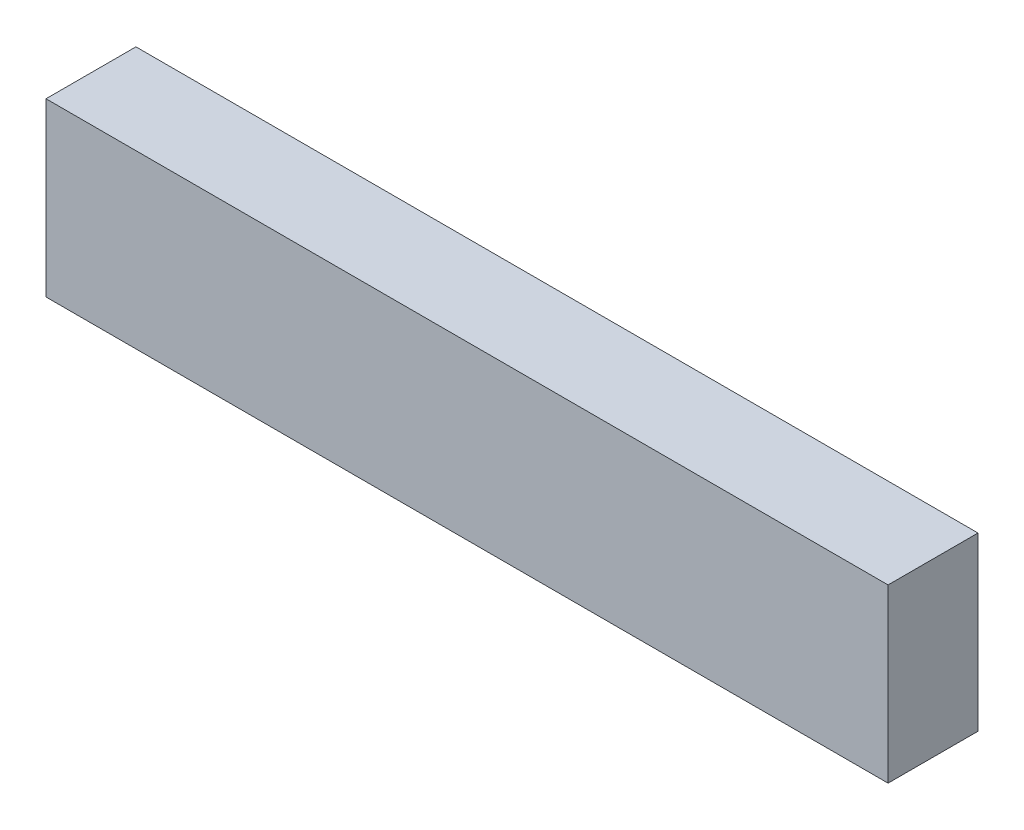
SolidWorks part; units mm, degrees
material "ABS"
ref_plane "Front Plane" through (0, 0, 0) normal (0, 0, 1) x (1, 0, 0)
ref_plane "Top Plane" through (0, 0, 0) normal (0, 1, 0) x (1, 0, 0)
ref_plane "Right Plane" through (0, 0, 0) normal (1, 0, 0) x (0, 0, -1)
sketch "Sketch2" plane through (0, 0, 0) normal (0, 1, 0) x (1, 0, 0)
  line L1 (0, 0) -> (327.025, 0)
  line L2 (0, 0) -> (0, 34.925)
  line L3 (0, 34.925) -> (327.025, 34.925)
  line L4 (327.025, 0) -> (327.025, 34.925)
  dimension "D1" = 327.025
  dimension "D2" = 34.925
extrude "Boss-Extrude1" add sketch "Sketch2" along normal blind 66.675
